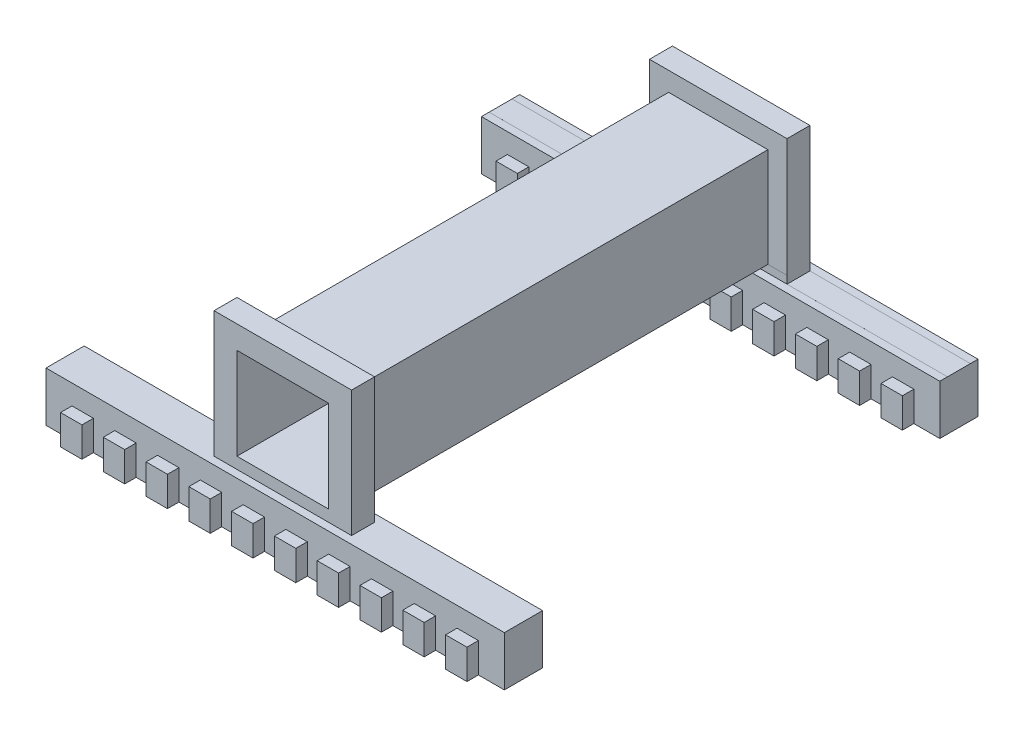
SolidWorks part; units mm, degrees
ref_plane "前视基准面" through (0, 0, 0) normal (0, 0, 1) x (1, 0, 0)
ref_plane "上视基准面" through (0, 0, 0) normal (0, 1, 0) x (1, 0, 0)
ref_plane "右视基准面" through (0, 0, 0) normal (1, 0, 0) x (0, 0, -1)
sketch "草图1" plane through (0, 0, 0) normal (0, 0, 1) x (1, 0, 0)
  line L0 (-30, -12.5) -> (30, -12.5)
  line L5 (-6.5, -6.5) -> (6.5, -6.5)
  line L6 (-6.5, -6.5) -> (-6.5, 6.5)
  line L7 (-6.5, 6.5) -> (6.5, 6.5)
  line L8 (6.5, -6.5) -> (6.5, 6.5)
  line L9 (-6.5, -6.5) -> (6.5, 6.5) construction
  line L10 (-6.5, 6.5) -> (6.5, -6.5) construction
  line L11 (-30, -6.5) -> (30, -6.5)
  line L12 (-30, -6.5) -> (-30, -12.5)
  line L14 (30, -6.5) -> (30, -12.5)
  point P0 (0, 0)
  dimension "D1" = 13
  dimension "D2" = 13
extrude "凸台-拉伸1" add sketch "草图1" along normal mid plane 60 contours L14 L11 L5 L12 L0 | L5 L8 L7 L6
sketch "草图2" plane through (0, 0, 30) normal (0, 0, 1) x (1, 0, 0)
  line L0 (-6.5, -6.5) -> (-6.5, 6.5)
  line L1 (-6.5, 6.5) -> (6.5, 6.5) construction
  line L2 (-6.5, -6.5) -> (-6.5, 6.5) construction
  line L3 (-6.5, 6.5) -> (6.5, 6.5)
  line L4 (6.5, 6.5) -> (6.5, -6.5)
  line L5 (6, 6) -> (6, -6)
  line L6 (-6, -6) -> (6, -6)
  line L7 (-6, -6) -> (-6, 6)
  line L8 (-6, 6) -> (6, 6)
  line L16 (-6.5, -6.5) -> (6.5, -6.5)
  dimension "D1" = 0.5
extrude "切除-拉伸2" cut sketch "草图2" against normal blind 60 contours L8 L7 L6 L5
sketch "草图4" plane through (0, 0, 30) normal (0, 0, 1) x (1, 0, 0)
  line L13 (-9, -8.8525) -> (9, -8.8525)
  line L16 (9, 9) -> (-9, 9)
  line L17 (-9, 9) -> (-9, -6.5)
  line L18 (9, -6.5) -> (9, 9)
  line L19 (9, 9) -> (-9, 9)
  line L20 (-9, 9) -> (-9, -8.8525)
  line L21 (9, -8.8525) -> (9, 9)
  dimension "D1" = 2.5
extrude "凸台-拉伸2" add sketch "草图4" against normal blind 3
sketch "草图6" plane through (0, 0, 27) normal (0, 0, -1) x (-1, 0, 0)
  line L0 (-6, -6) -> (6, -6)
  line L1 (-6, -6) -> (6, -6) construction
  line L2 (6, -6) -> (6, 6)
  line L3 (6, 6) -> (-6, 6)
  line L4 (-6, 6) -> (-6, -6)
extrude "切除-拉伸3" cut sketch "草图6" against normal blind 3
sketch "草图7" plane through (0, 0, 30) normal (0, 0, 1) x (1, 0, 0)
  line L8 (30, -6.5) -> (9, -6.5)
  line L9 (9, -6.5) -> (9, 9)
  line L10 (9, 9) -> (-9, 9)
  line L11 (-9, 9) -> (-9, -6.5)
  line L12 (-9, -6.5) -> (-30, -6.5)
  line L13 (-30, -6.5) -> (-30, -12.5)
  line L14 (-30, -12.5) -> (30, -12.5)
  line L15 (30, -12.5) -> (30, -6.5)
  line L16 (30, -6.5) -> (9, -6.5)
  line L17 (9, -6.5) -> (9, 9)
  line L18 (9, 9) -> (-9, 9)
  line L19 (-9, 9) -> (-9, -6.5)
  line L20 (-9, -6.5) -> (-30, -6.5)
  line L21 (-30, -6.5) -> (-30, -12.5)
  line L22 (-30, -12.5) -> (30, -12.5)
  line L23 (30, -12.5) -> (30, -6.5)
  dimension "D1" = 0
sketch "草图9" plane through (0, 0, -30) normal (0, 0, -1) x (-1, 0, 0)
  line L0 (-6, 6) -> (-6, -6)
  line L1 (-9, -9) -> (9, -9)
  line L8 (-6, -6) -> (6, -6)
  line L9 (6, -6) -> (6, 6)
  line L10 (6, 6) -> (-6, 6)
  line L11 (9, -6.5) -> (9, 9)
  line L12 (9, 9) -> (-9, 9)
  line L13 (-9, 9) -> (-9, -6.5)
  line L14 (9, -9) -> (9, 9)
  line L15 (9, 9) -> (-9, 9)
  line L16 (-9, 9) -> (-9, -9)
  dimension "D2" = 2.5
extrude "凸台-拉伸3" add sketch "草图9" against normal blind 3
sketch "草图10" plane through (30, 0, 0) normal (1, 0, 0) x (0, 0, -1)
  line L0 (-30, -6.5) -> (-24.5, -6.5)
  line L1 (-30, -6.5) -> (30, -6.5) construction
  line L2 (-24.5, -6.5) -> (-24.5, -12.5)
  line L3 (-30, -12.5) -> (30, -12.5) construction
  line L4 (-24.5, -12.5) -> (-30, -12.5)
  line L5 (30, -12.5) -> (24.5, -12.5)
  line L6 (24.5, -12.5) -> (24.5, -6.5)
  line L7 (24.5, -6.5) -> (29.5487, -6.5)
  line L8 (-24.5, -6.5) -> (24.5, -6.5)
  line L9 (-24.5, -12.5) -> (24.5, -12.5)
  line M6 (30, -6.5) -> (-30, -6.5)
  line M8 (-30, -12.5) -> (30, -12.5)
extrude "切除-拉伸4" cut sketch "草图10" against normal blind 60 contours L6 L2 M8 M6
sketch "草图13" plane through (30, 0, 0) normal (1, 0, 0) x (0, 0, -1)
  line L0 (-30, -6.5) -> (-36, -6.5)
  line L1 (-30, -12.5) -> (-36, -12.5)
  line L2 (-36, -12.5) -> (-36, -6.5)
  line L3 (-30, -12.5) -> (-30, -6.5) construction
  line L4 (-30, -6.5) -> (-30, -12.5)
extrude "凸台-拉伸4" add sketch "草图13" against normal blind 60
sketch "草图14" plane through (30, 0, 0) normal (1, 0, 0) x (0, 0, -1)
  line L0 (-36, -12.5) -> (-32.5, -12.5)
  line L1 (-36, -12.5) -> (-24.5, -12.5) construction
  line L2 (-32.5, -12.5) -> (-32.5, -6.5)
  line L3 (-36, -6.5) -> (-24.5, -6.5) construction
  line L4 (-32.5, -6.5) -> (-36, -6.5)
  line L5 (-36, -6.5) -> (-36, -12.5)
extrude "切除-拉伸5" cut sketch "草图14" against normal blind 60
sketch "草图15" plane through (30, 0, 0) normal (1, 0, 0) x (0, 0, -1)
  line L0 (30, -6.5) -> (32.5, -6.5)
  line L1 (30, -12.5) -> (32.5, -12.5)
  line L2 (32.5, -12.5) -> (32.5, -6.5)
  line L3 (30, -6.5) -> (30, -12.5)
extrude "凸台-拉伸5" add sketch "草图15" against normal blind 60
sketch "草图16" plane through (-30, 0, 0) normal (-1, 0, 0) x (0, 0, 1)
  line L0 (-32.5, -12.5) -> (-32.5, -14)
  line L1 (-24.5, -12.5) -> (-24.5, -14)
  line L2 (-24.5, -12.5) -> (-24.5, -6.5) construction
  line L3 (-24.5, -14) -> (-32.5, -14)
  line L4 (-32.5, -12.5) -> (-24.5, -12.5)
extrude "凸台-拉伸6" add sketch "草图16" against normal blind 60 contours L3 L0 L4 L1
sketch "草图17" plane through (-30, 0, 0) normal (-1, 0, 0) x (0, 0, 1)
  line L0 (24.5, -12.5) -> (24.5, -14)
  line L1 (32.5, -12.5) -> (32.5, -14)
  line L2 (32.5, -14) -> (24.5, -14)
  line L3 (24.5, -12.5) -> (32.5, -12.5)
extrude "凸台-拉伸7" add sketch "草图17" against normal blind 60
sketch "草图18" plane through (-30, 0, 0) normal (-1, 0, 0) x (0, 0, 1)
  line L1 (30, -6.5) -> (30, -7.5)
  line L2 (30, -6.5) -> (30, -12.5) construction
  line L3 (32.5, -6.5) -> (24.5, -6.5) construction
  line L4 (30, -7.5) -> (32.5, -7.5)
  line L5 (32.5, -14) -> (32.5, -6.5) construction
  line L6 (32.5, -7.5) -> (32.5, -6.5)
  line L7 (32.5, -6.5) -> (30, -6.5)
extrude "切除-拉伸6" cut sketch "草图18" against normal blind 60
sketch "草图21" plane through (-30, 0, 0) normal (-1, 0, 0) x (0, 0, 1)
  line L0 (24.5, -6.5) -> (27, -6.5)
  line L1 (30, -6.5) -> (24.5, -6.5) construction
  line L2 (24.5, -6.5) -> (24.5, -7.5)
  line L3 (24.5, -6.5) -> (24.5, -14) construction
  line L4 (24.5, -7.5) -> (27, -7.5)
  line L5 (27, -7.5) -> (27, -6.5)
extrude "切除-拉伸7" cut sketch "草图21" against normal blind 60
sketch "草图22" plane through (0, -6.5, 0) normal (0, 1, 0) x (1, 0, 0)
  line L0 (-9, -30) -> (-9, -27)
  line L1 (-9, -27) -> (-29.8326, -27)
  line L2 (-9, -27) -> (-30, -27) construction
sketch "草图24" plane through (0, -6.5, 0) normal (0, 1, 0) x (1, 0, 0)
  line L0 (-9, -27) -> (-30, -27)
  line L1 (-9, -27) -> (-30, -27) construction
  line L2 (-30, -30) -> (-30, -27) construction
  line L3 (-30, -27) -> (-30, -30.0585)
  line L4 (-30, -30.0585) -> (-9, -30)
  line L5 (-9, -30) -> (-30, -30) construction
  line L6 (-9, -30) -> (-9, -27)
extrude "切除-拉伸9" cut sketch "草图24" against normal blind 1
sketch "草图25" plane through (0, -6.5, 0) normal (0, 1, 0) x (1, 0, 0)
  line L0 (9, -30) -> (30, -30)
  line L1 (30, -30) -> (9, -30) construction
  line L2 (9, -30) -> (9, -27) construction
  line L3 (30, -30) -> (30, -27)
  line L4 (30, -30) -> (30, -27) construction
  line L5 (30, -27) -> (9, -27)
  line L6 (9, -27) -> (9, -30)
extrude "切除-拉伸10" cut sketch "草图25" against normal blind 1
sketch "草图26" plane through (30, 0, 0) normal (1, 0, 0) x (0, 0, -1)
  line L0 (24.5, -6.5) -> (32.5, -6.5) construction
  line L1 (32.5, -6.5) -> (32.5, -7.5004)
  line L2 (32.5, -14) -> (32.5, -6.5) construction
  line L3 (32.5, -7.5004) -> (30, -7.5004)
  line L4 (30, -7.5004) -> (30, -6.5)
  line L5 (30, -6.5) -> (32.5, -6.5)
  line L6 (24.5, -6.5) -> (24.5, -7.5004)
  line L7 (24.5, -14) -> (24.5, -6.5) construction
  line L8 (24.5, -7.5004) -> (27.0046, -7.5004)
  line L9 (27.0046, -7.5004) -> (27.0046, -6.5)
  line L10 (27.0046, -6.5) -> (24.5, -6.5)
extrude "切除-拉伸11" cut sketch "草图26" against normal blind 60
sketch "草图27" plane through (0, -6.5, 0) normal (0, 1, 0) x (1, 0, 0)
  line L0 (9, 30) -> (9, 27.0046)
  line L1 (9, 27.0046) -> (30, 27.0046)
  line L2 (30, 27.0046) -> (30, 30)
  line L3 (30, 27.0046) -> (30, 30) construction
  line L4 (9, 30) -> (30, 30) construction
  line L5 (30, 30) -> (9, 30)
  line L6 (-30, 27.0046) -> (-30, 30)
  line L7 (-30, 27.0046) -> (-30, 30) construction
  line L8 (-30, 30) -> (-9, 30)
  line L9 (-9, 30) -> (-9, 27.0046)
  line L10 (-9, 27.0046) -> (-30, 27.0046)
extrude "切除-拉伸12" cut sketch "草图27" against normal blind 1
sketch "草图28" plane through (0, 0, 32.5) normal (0, 0, 1) x (1, 0, 0)
  line L0 (-30, -14) -> (-26.6, -14)
  line L1 (30, -14) -> (-30, -14) construction
  line L2 (-26.6, -14) -> (-26.6, -10.0956)
  line L3 (-26.6, -10.0956) -> (-23.8, -10.0956)
  line L4 (-23.8, -10.0956) -> (-23.8, -14)
  line L5 (-23.8, -14) -> (-21, -14)
  line L6 (-21, -14) -> (-21, -10.0956)
  line L7 (-21, -10.0956) -> (-18.2, -10.0956)
  line L8 (-18.2, -10.0956) -> (-18.2, -14)
  line L9 (-18.2, -14) -> (-15.4, -14)
  line L10 (-15.4, -14) -> (-15.4, -10.0956)
  line L11 (-15.4, -10.0956) -> (-12.6, -10.0956)
  line L12 (-12.6, -10.0956) -> (-12.6, -14)
  line L13 (-12.6, -14) -> (-9.8, -14)
  line L14 (-9.8, -14) -> (-9.8, -10.0956)
  line L15 (-9.8, -10.0956) -> (-7, -10.0956)
  line L16 (-7, -10.0956) -> (-7, -14)
  line L17 (-7, -14) -> (-4.2, -14)
  line L18 (-4.2, -14) -> (-4.2, -10.0956)
  line L19 (-4.2, -10.0956) -> (-1.4001, -10.0956)
  line L20 (-1.4001, -10.0956) -> (-1.4001, -14)
  line L21 (-1.4001, -14) -> (1.3999, -14)
  line L22 (1.3999, -14) -> (1.3999, -10.0956)
  line L23 (1.3999, -10.0956) -> (4.1997, -10.0956)
  line L24 (4.1997, -10.0956) -> (4.1997, -14)
  line L25 (4.1997, -14) -> (6.9997, -14)
  line L26 (6.9997, -14) -> (6.9997, -10.0956)
  line L27 (6.9997, -10.0956) -> (9.7997, -10.0956)
  line L28 (9.7997, -10.0956) -> (9.7997, -14)
  line L29 (9.7997, -14) -> (12.5997, -14)
  line L30 (12.5997, -14) -> (12.5997, -10.0956)
  line L31 (12.5997, -10.0956) -> (15.4037, -10.0956)
  line L32 (15.4037, -10.0956) -> (15.4037, -14)
  line L33 (15.4037, -14) -> (18.2025, -14)
  line L34 (18.2025, -14) -> (18.2025, -10.0956)
  line L35 (18.2025, -10.0956) -> (21.0025, -10.0956)
  line L36 (21.0025, -10.0956) -> (21.0025, -14)
  line L37 (21.0025, -14) -> (23.804, -14)
  line L38 (23.804, -14) -> (23.804, -10.0956)
  line L39 (23.804, -10.0956) -> (26.6026, -10.0956)
  line L40 (26.6026, -10.0956) -> (26.6026, -14)
  line L41 (26.6026, -14) -> (30, -14)
  line L42 (30, -14) -> (30, -7.5) construction
  line L43 (30, -14) -> (30, -10.0956)
  line L44 (-26.6, -14) -> (-23.8, -14)
  line L45 (-21, -14) -> (-18.2, -14)
  line L46 (-15.4, -14) -> (-12.6, -14)
  line L47 (-9.8, -14) -> (-7, -14)
  line L48 (-4.2, -14) -> (-1.4001, -14)
  line L49 (1.3999, -14) -> (4.1997, -14)
  line L50 (6.9997, -14) -> (9.7997, -14)
  line L51 (12.5997, -14) -> (15.4037, -14)
  line L52 (18.2025, -14) -> (21.0025, -14)
  line L53 (23.804, -14) -> (26.6026, -14)
  line L58 (-30, -7.5) -> (-30, -14)
  line L59 (30, -7.5) -> (-30, -7.5)
  line L60 (30, -14) -> (30, -7.5)
  line L61 (-30, -14) -> (30, -14)
  line L62 (-30, -7.5) -> (-30, -14)
  line L63 (30, -7.5) -> (-30, -7.5)
  line L64 (30, -14) -> (30, -7.5)
  line L65 (-30, -14) -> (30, -14)
  line M15 (30, -14) -> (30, -7.5)
  line M16 (30, -7.5) -> (-30, -7.5)
  line M17 (-30, -7.5) -> (-30, -14)
  line M18 (-30, -14) -> (30, -14)
  dimension "D1" = 0
extrude "切除-拉伸14" cut sketch "草图28" against normal blind 1.5 contours L39 L40 L2 L3 L4 L6 L7 L8 L10 L11 L12 L14 L15 L16 L18 L19 L20 L22 L23 L24 L26 L27 L28 L30 L31 L32 L34 L35 L36 L38 M18 M15 M16 M17
sketch "草图29" plane through (0, 0, 24.5) normal (0, 0, -1) x (-1, 0, 0)
  line L0 (-26.6026, -10.0956) -> (-23.804, -10.0956) construction
  line L1 (-23.804, -10.0956) -> (-23.804, -14) construction
  line L2 (-23.804, -14) -> (-26.6026, -14) construction
  line L3 (-26.6026, -14) -> (-26.6026, -10.0956) construction
  line L4 (30, -14) -> (30, -7.5)
  line L5 (30, -7.5) -> (-30, -7.5)
  line L6 (-30, -7.5) -> (-30, -14)
  line L7 (-30, -14) -> (30, -14)
  line L8 (30, -14) -> (30, -7.5)
  line L9 (30, -7.5) -> (-30, -7.5)
  line L10 (-30, -7.5) -> (-30, -14)
  line L11 (-30, -14) -> (30, -14)
  line L12 (23.8, -14) -> (26.6, -14)
  line L13 (23.8, -10.0956) -> (23.8, -14)
  line L14 (26.6, -10.0956) -> (23.8, -10.0956)
  line L15 (26.6, -14) -> (26.6, -10.0956)
  line L16 (23.8, -14) -> (26.6, -14)
  line L17 (23.8, -10.0956) -> (23.8, -14)
  line L18 (26.6, -10.0956) -> (23.8, -10.0956)
  line L19 (26.6, -14) -> (26.6, -10.0956)
  line L20 (-18.2025, -14) -> (-21.0025, -14) construction
  line L21 (-21.0025, -14) -> (-21.0025, -10.0956) construction
  line L22 (-21.0025, -10.0956) -> (-18.2025, -10.0956) construction
  line L23 (-18.2025, -10.0956) -> (-18.2025, -14) construction
  line L24 (-12.5997, -14) -> (-15.4037, -14) construction
  line L25 (-15.4037, -14) -> (-15.4037, -10.0956) construction
  line L26 (-15.4037, -10.0956) -> (-12.5997, -10.0956) construction
  line L27 (-12.5997, -10.0956) -> (-12.5997, -14) construction
  line L28 (-6.9997, -14) -> (-9.7997, -14) construction
  line L29 (-9.7997, -14) -> (-9.7997, -10.0956) construction
  line L30 (-9.7997, -10.0956) -> (-6.9997, -10.0956) construction
  line L31 (-6.9997, -10.0956) -> (-6.9997, -14) construction
  line L32 (-1.3999, -14) -> (-4.1997, -14) construction
  line L33 (-4.1997, -14) -> (-4.1997, -10.0956) construction
  line L34 (-4.1997, -10.0956) -> (-1.3999, -10.0956) construction
  line L35 (-1.3999, -10.0956) -> (-1.3999, -14) construction
  line L36 (4.2, -14) -> (1.4001, -14) construction
  line L37 (1.4001, -14) -> (1.4001, -10.0956) construction
  line L38 (1.4001, -10.0956) -> (4.2, -10.0956) construction
  line L39 (4.2, -10.0956) -> (4.2, -14) construction
  line L40 (9.8, -14) -> (7, -14) construction
  line L41 (7, -14) -> (7, -10.0956) construction
  line L42 (7, -10.0956) -> (9.8, -10.0956) construction
  line L43 (9.8, -10.0956) -> (9.8, -14) construction
  line L44 (15.4, -14) -> (12.6, -14) construction
  line L45 (12.6, -14) -> (12.6, -10.0956) construction
  line L46 (12.6, -10.0956) -> (15.4, -10.0956) construction
  line L47 (15.4, -10.0956) -> (15.4, -14) construction
  line L48 (21, -14) -> (18.2, -14) construction
  line L49 (18.2, -14) -> (18.2, -10.0956) construction
  line L50 (18.2, -10.0956) -> (21, -10.0956) construction
  line L51 (21, -10.0956) -> (21, -14) construction
  line L52 (-26.6026, -10.0956) -> (-23.804, -10.0956)
  line L53 (-23.804, -10.0956) -> (-23.804, -14)
  line L54 (-23.804, -14) -> (-26.6026, -14)
  line L55 (-26.6026, -14) -> (-26.6026, -10.0956)
  line L56 (-18.2025, -14) -> (-21.0025, -14)
  line L57 (-21.0025, -14) -> (-21.0025, -10.0956)
  line L58 (-21.0025, -10.0956) -> (-18.2025, -10.0956)
  line L59 (-18.2025, -10.0956) -> (-18.2025, -14)
  line L60 (-12.5997, -14) -> (-15.4037, -14)
  line L61 (-15.4037, -14) -> (-15.4037, -10.0956)
  line L62 (-15.4037, -10.0956) -> (-12.5997, -10.0956)
  line L63 (-12.5997, -10.0956) -> (-12.5997, -14)
  line L64 (-6.9997, -14) -> (-9.7997, -14)
  line L65 (-9.7997, -14) -> (-9.7997, -10.0956)
  line L66 (-9.7997, -10.0956) -> (-6.9997, -10.0956)
  line L67 (-6.9997, -10.0956) -> (-6.9997, -14)
  line L68 (-1.3999, -14) -> (-4.1997, -14)
  line L69 (-4.1997, -14) -> (-4.1997, -10.0956)
  line L70 (-4.1997, -10.0956) -> (-1.3999, -10.0956)
  line L71 (-1.3999, -10.0956) -> (-1.3999, -14)
  line L72 (4.2, -14) -> (1.4001, -14)
  line L73 (1.4001, -14) -> (1.4001, -10.0956)
  line L74 (1.4001, -10.0956) -> (4.2, -10.0956)
  line L75 (4.2, -10.0956) -> (4.2, -14)
  line L76 (9.8, -14) -> (7, -14)
  line L77 (7, -14) -> (7, -10.0956)
  line L78 (7, -10.0956) -> (9.8, -10.0956)
  line L79 (9.8, -10.0956) -> (9.8, -14)
  line L80 (15.4, -14) -> (12.6, -14)
  line L81 (12.6, -14) -> (12.6, -10.0956)
  line L82 (12.6, -10.0956) -> (15.4, -10.0956)
  line L83 (15.4, -10.0956) -> (15.4, -14)
  line L84 (21, -14) -> (18.2, -14)
  line L85 (18.2, -14) -> (18.2, -10.0956)
  line L86 (18.2, -10.0956) -> (21, -10.0956)
  line L87 (21, -10.0956) -> (21, -14)
  line M9 (30, -14) -> (30, -7.5)
  line M10 (30, -7.5) -> (-30, -7.5)
  line M11 (-30, -7.5) -> (-30, -14)
  line M12 (-30, -14) -> (30, -14)
  dimension "D1" = 0
  dimension "D2" = 0
extrude "切除-拉伸15" cut sketch "草图29" against normal blind 1.5 contours L86 L87 L11 L17 L18 L19 L55 L52 L53 L57 L58 L59 L61 L62 L63 L65 L66 L67 L69 L70 L71 L73 L74 L75 L77 L78 L79 L81 L82 L83 L85 M12 M9 M10 M11
sketch "草图30" plane through (0, 0, -24.5) normal (0, 0, 1) x (1, 0, 0)
  line L0 (-26.6, -14) -> (-26.6, -10.0956) construction
  line L1 (-26.6, -10.0956) -> (-23.8, -10.0956) construction
  line L2 (-23.8, -10.0956) -> (-23.8, -14) construction
  line L3 (-23.8, -14) -> (-26.6, -14) construction
  line L4 (30, -14) -> (30, -7.5004)
  line L5 (30, -7.5004) -> (-30, -7.5004)
  line L6 (-30, -7.5004) -> (-30, -14)
  line L7 (-30, -14) -> (30, -14)
  line L8 (30, -14) -> (30, -7.5004)
  line L9 (30, -7.5004) -> (-30, -7.5004)
  line L10 (-30, -7.5004) -> (-30, -14)
  line L11 (-30, -14) -> (30, -14)
  line L12 (12.5997, -14) -> (15.4037, -14)
  line L13 (12.5997, -10.0956) -> (12.5997, -14)
  line L14 (15.4037, -10.0956) -> (12.5997, -10.0956)
  line L15 (15.4037, -14) -> (15.4037, -10.0956)
  line L16 (12.5997, -14) -> (15.4037, -14)
  line L17 (12.5997, -10.0956) -> (12.5997, -14)
  line L18 (15.4037, -10.0956) -> (12.5997, -10.0956)
  line L19 (15.4037, -14) -> (15.4037, -10.0956)
  line L20 (-21, -10.0956) -> (-18.2, -10.0956) construction
  line L21 (-18.2, -10.0956) -> (-18.2, -14) construction
  line L22 (-18.2, -14) -> (-21, -14) construction
  line L23 (-21, -14) -> (-21, -10.0956) construction
  line L24 (-12.6, -14) -> (-15.4, -14) construction
  line L25 (-15.4, -14) -> (-15.4, -10.0956) construction
  line L26 (-15.4, -10.0956) -> (-12.6, -10.0956) construction
  line L27 (-12.6, -10.0956) -> (-12.6, -14) construction
  line L28 (-7, -14) -> (-9.8, -14) construction
  line L29 (-9.8, -14) -> (-9.8, -10.0956) construction
  line L30 (-9.8, -10.0956) -> (-7, -10.0956) construction
  line L31 (-7, -10.0956) -> (-7, -14) construction
  line L32 (-1.4001, -14) -> (-4.2, -14) construction
  line L33 (-4.2, -14) -> (-4.2, -10.0956) construction
  line L34 (-4.2, -10.0956) -> (-1.4001, -10.0956) construction
  line L35 (-1.4001, -10.0956) -> (-1.4001, -14) construction
  line L36 (4.1997, -14) -> (1.3999, -14) construction
  line L37 (1.3999, -14) -> (1.3999, -10.0956) construction
  line L38 (1.3999, -10.0956) -> (4.1997, -10.0956) construction
  line L39 (4.1997, -10.0956) -> (4.1997, -14) construction
  line L40 (9.7997, -14) -> (6.9997, -14) construction
  line L41 (6.9997, -14) -> (6.9997, -10.0956) construction
  line L42 (6.9997, -10.0956) -> (9.7997, -10.0956) construction
  line L43 (9.7997, -10.0956) -> (9.7997, -14) construction
  line L44 (15.4037, -14) -> (12.5997, -14) construction
  line L45 (12.5997, -14) -> (12.5997, -10.0956) construction
  line L46 (12.5997, -10.0956) -> (15.4037, -10.0956) construction
  line L47 (15.4037, -10.0956) -> (15.4037, -14) construction
  line L48 (21.0025, -14) -> (18.2025, -14) construction
  line L49 (18.2025, -14) -> (18.2025, -10.0956) construction
  line L50 (18.2025, -10.0956) -> (21.0025, -10.0956) construction
  line L51 (21.0025, -10.0956) -> (21.0025, -14) construction
  line L52 (26.6026, -14) -> (23.804, -14) construction
  line L53 (23.804, -14) -> (23.804, -10.0956) construction
  line L54 (23.804, -10.0956) -> (26.6026, -10.0956) construction
  line L55 (26.6026, -10.0956) -> (26.6026, -14) construction
  line L56 (-26.6, -14) -> (-26.6, -10.0956)
  line L57 (-26.6, -10.0956) -> (-23.8, -10.0956)
  line L58 (-23.8, -10.0956) -> (-23.8, -14)
  line L59 (-23.8, -14) -> (-26.6, -14)
  line L60 (-21, -10.0956) -> (-18.2, -10.0956)
  line L61 (-18.2, -10.0956) -> (-18.2, -14)
  line L62 (-18.2, -14) -> (-21, -14)
  line L63 (-21, -14) -> (-21, -10.0956)
  line L64 (-12.6, -14) -> (-15.4, -14)
  line L65 (-15.4, -14) -> (-15.4, -10.0956)
  line L66 (-15.4, -10.0956) -> (-12.6, -10.0956)
  line L67 (-12.6, -10.0956) -> (-12.6, -14)
  line L68 (-7, -14) -> (-9.8, -14)
  line L69 (-9.8, -14) -> (-9.8, -10.0956)
  line L70 (-9.8, -10.0956) -> (-7, -10.0956)
  line L71 (-7, -10.0956) -> (-7, -14)
  line L72 (-1.4001, -14) -> (-4.2, -14)
  line L73 (-4.2, -14) -> (-4.2, -10.0956)
  line L74 (-4.2, -10.0956) -> (-1.4001, -10.0956)
  line L75 (-1.4001, -10.0956) -> (-1.4001, -14)
  line L76 (4.1997, -14) -> (1.3999, -14)
  line L77 (1.3999, -14) -> (1.3999, -10.0956)
  line L78 (1.3999, -10.0956) -> (4.1997, -10.0956)
  line L79 (4.1997, -10.0956) -> (4.1997, -14)
  line L80 (9.7997, -14) -> (6.9997, -14)
  line L81 (6.9997, -14) -> (6.9997, -10.0956)
  line L82 (6.9997, -10.0956) -> (9.7997, -10.0956)
  line L83 (9.7997, -10.0956) -> (9.7997, -14)
  line L84 (15.4037, -14) -> (12.5997, -14)
  line L85 (12.5997, -14) -> (12.5997, -10.0956)
  line L86 (12.5997, -10.0956) -> (15.4037, -10.0956)
  line L87 (15.4037, -10.0956) -> (15.4037, -14)
  line L88 (21.0025, -14) -> (18.2025, -14)
  line L89 (18.2025, -14) -> (18.2025, -10.0956)
  line L90 (18.2025, -10.0956) -> (21.0025, -10.0956)
  line L91 (21.0025, -10.0956) -> (21.0025, -14)
  line L92 (26.6026, -14) -> (23.804, -14)
  line L93 (23.804, -14) -> (23.804, -10.0956)
  line L94 (23.804, -10.0956) -> (26.6026, -10.0956)
  line L95 (26.6026, -10.0956) -> (26.6026, -14)
  line M9 (30, -14) -> (30, -7.5004)
  line M10 (30, -7.5004) -> (-30, -7.5004)
  line M11 (-30, -7.5004) -> (-30, -14)
  line M12 (-30, -14) -> (30, -14)
  dimension "D1" = 0
  dimension "D2" = 0
sketch "草图31" plane through (0, 0, -32.5) normal (0, 0, -1) x (-1, 0, 0)
  line L0 (26.6, -14) -> (26.6, -10.0956) construction
  line L1 (26.6, -10.0956) -> (23.8, -10.0956) construction
  line L2 (23.8, -10.0956) -> (23.8, -14) construction
  line L3 (23.8, -14) -> (26.6, -14) construction
  line L4 (30, -7.5004) -> (-30, -7.5004)
  line L5 (-30, -7.5004) -> (-30, -14)
  line L6 (-30, -14) -> (30, -14)
  line L7 (30, -14) -> (30, -7.5004)
  line L8 (30, -7.5004) -> (-30, -7.5004)
  line L9 (-30, -7.5004) -> (-30, -14)
  line L10 (-30, -14) -> (30, -14)
  line L11 (30, -14) -> (30, -7.5004)
  line L12 (21, -10.0956) -> (18.2, -10.0956) construction
  line L13 (18.2, -10.0956) -> (18.2, -14) construction
  line L14 (18.2, -14) -> (21, -14) construction
  line L15 (21, -14) -> (21, -10.0956) construction
  line L16 (12.6, -14) -> (15.4, -14) construction
  line L17 (15.4, -14) -> (15.4, -10.0956) construction
  line L18 (15.4, -10.0956) -> (12.6, -10.0956) construction
  line L19 (12.6, -10.0956) -> (12.6, -14) construction
  line L20 (7, -14) -> (9.8, -14) construction
  line L21 (9.8, -14) -> (9.8, -10.0956) construction
  line L22 (9.8, -10.0956) -> (7, -10.0956) construction
  line L23 (7, -10.0956) -> (7, -14) construction
  line L24 (1.4001, -14) -> (4.2, -14) construction
  line L25 (4.2, -14) -> (4.2, -10.0956) construction
  line L26 (4.2, -10.0956) -> (1.4001, -10.0956) construction
  line L27 (1.4001, -10.0956) -> (1.4001, -14) construction
  line L28 (-4.1997, -14) -> (-1.3999, -14) construction
  line L29 (-1.3999, -14) -> (-1.3999, -10.0956) construction
  line L30 (-1.3999, -10.0956) -> (-4.1997, -10.0956) construction
  line L31 (-4.1997, -10.0956) -> (-4.1997, -14) construction
  line L32 (-9.7997, -14) -> (-6.9997, -14) construction
  line L33 (-6.9997, -14) -> (-6.9997, -10.0956) construction
  line L34 (-6.9997, -10.0956) -> (-9.7997, -10.0956) construction
  line L35 (-9.7997, -10.0956) -> (-9.7997, -14) construction
  line L36 (-15.4037, -14) -> (-12.5997, -14) construction
  line L37 (-12.5997, -14) -> (-12.5997, -10.0956) construction
  line L38 (-12.5997, -10.0956) -> (-15.4037, -10.0956) construction
  line L39 (-15.4037, -10.0956) -> (-15.4037, -14) construction
  line L40 (-21.0025, -14) -> (-18.2025, -14) construction
  line L41 (-18.2025, -14) -> (-18.2025, -10.0956) construction
  line L42 (-18.2025, -10.0956) -> (-21.0025, -10.0956) construction
  line L43 (-21.0025, -10.0956) -> (-21.0025, -14) construction
  line L44 (-26.6026, -14) -> (-23.804, -14) construction
  line L45 (-23.804, -14) -> (-23.804, -10.0956) construction
  line L46 (-23.804, -10.0956) -> (-26.6026, -10.0956) construction
  line L47 (-26.6026, -10.0956) -> (-26.6026, -14) construction
  line L48 (26.6, -14) -> (26.6, -10.0956)
  line L49 (26.6, -10.0956) -> (23.8, -10.0956)
  line L50 (23.8, -10.0956) -> (23.8, -14)
  line L51 (23.8, -14) -> (26.6, -14)
  line L52 (21, -10.0956) -> (18.2, -10.0956)
  line L53 (18.2, -10.0956) -> (18.2, -14)
  line L54 (18.2, -14) -> (21, -14)
  line L55 (21, -14) -> (21, -10.0956)
  line L56 (12.6, -14) -> (15.4, -14)
  line L57 (15.4, -14) -> (15.4, -10.0956)
  line L58 (15.4, -10.0956) -> (12.6, -10.0956)
  line L59 (12.6, -10.0956) -> (12.6, -14)
  line L60 (7, -14) -> (9.8, -14)
  line L61 (9.8, -14) -> (9.8, -10.0956)
  line L62 (9.8, -10.0956) -> (7, -10.0956)
  line L63 (7, -10.0956) -> (7, -14)
  line L64 (1.4001, -14) -> (4.2, -14)
  line L65 (4.2, -14) -> (4.2, -10.0956)
  line L66 (4.2, -10.0956) -> (1.4001, -10.0956)
  line L67 (1.4001, -10.0956) -> (1.4001, -14)
  line L68 (-4.1997, -14) -> (-1.3999, -14)
  line L69 (-1.3999, -14) -> (-1.3999, -10.0956)
  line L70 (-1.3999, -10.0956) -> (-4.1997, -10.0956)
  line L71 (-4.1997, -10.0956) -> (-4.1997, -14)
  line L72 (-9.7997, -14) -> (-6.9997, -14)
  line L73 (-6.9997, -14) -> (-6.9997, -10.0956)
  line L74 (-6.9997, -10.0956) -> (-9.7997, -10.0956)
  line L75 (-9.7997, -10.0956) -> (-9.7997, -14)
  line L76 (-15.4037, -14) -> (-12.5997, -14)
  line L77 (-12.5997, -14) -> (-12.5997, -10.0956)
  line L78 (-12.5997, -10.0956) -> (-15.4037, -10.0956)
  line L79 (-15.4037, -10.0956) -> (-15.4037, -14)
  line L80 (-21.0025, -14) -> (-18.2025, -14)
  line L81 (-18.2025, -14) -> (-18.2025, -10.0956)
  line L82 (-18.2025, -10.0956) -> (-21.0025, -10.0956)
  line L83 (-21.0025, -10.0956) -> (-21.0025, -14)
  line L84 (-26.6026, -14) -> (-23.804, -14)
  line L85 (-23.804, -14) -> (-23.804, -10.0956)
  line L86 (-23.804, -10.0956) -> (-26.6026, -10.0956)
  line L87 (-26.6026, -10.0956) -> (-26.6026, -14)
  line M5 (30, -7.5004) -> (-30, -7.5004)
  line M6 (-30, -7.5004) -> (-30, -14)
  line M7 (-30, -14) -> (30, -14)
  line M8 (30, -14) -> (30, -7.5004)
  dimension "D1" = 0
extrude "切除-拉伸16" cut sketch "草图31" against normal blind 1.5 contours L87 L86 L85 L83 L82 L81 L79 L78 L77 L75 L74 L73 L71 L70 L69 L67 L66 L65 L63 L62 L61 L59 L58 L57 L53 L52 L55 L50 L49 L48 L10 M7 M8 M5 M6
extrude "切除-拉伸17" cut sketch "草图30" against normal blind 1.5 contours L94 L95 L56 L57 L58 L63 L60 L61 L11 L65 L66 L67 L69 L70 L71 L73 L74 L75 L77 L78 L79 L81 L82 L83 L17 L18 L19 L89 L90 L91 L93 M12 M9 M10 M11
